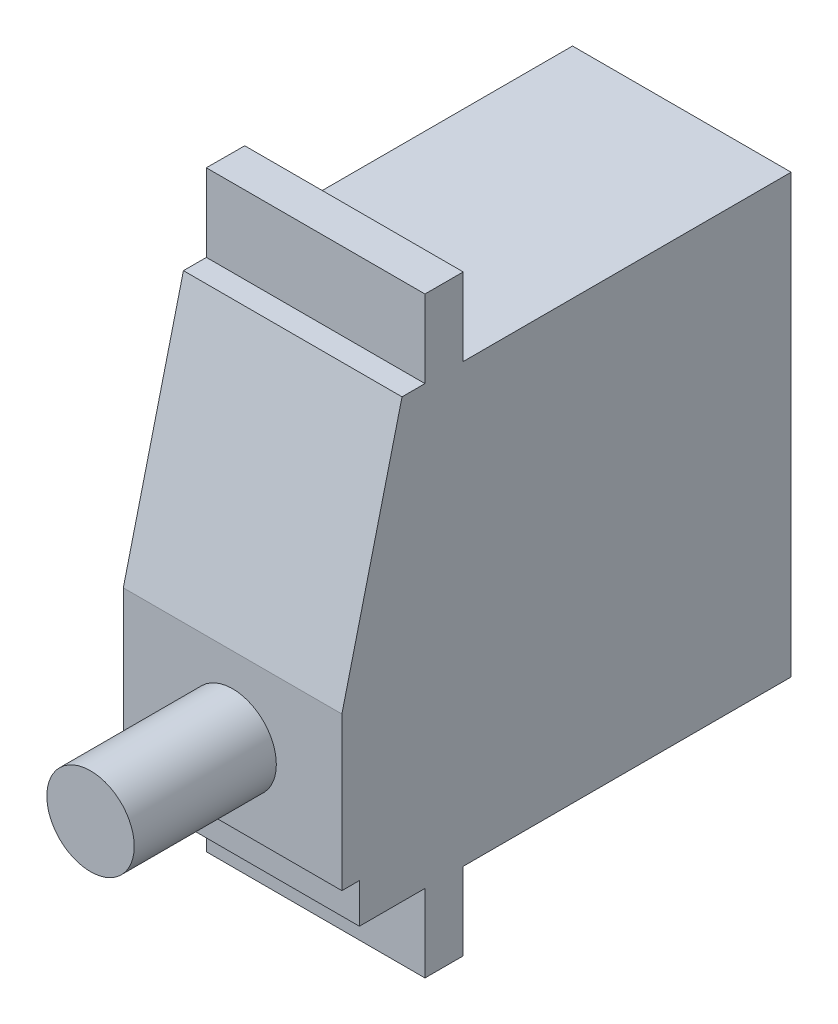
SolidWorks part; units mm, degrees
ref_plane "Front Plane" through (0, 0, 0) normal (0, 0, 1) x (1, 0, 0)
ref_plane "Top Plane" through (0, 0, 0) normal (0, 1, 0) x (1, 0, 0)
ref_plane "Right Plane" through (0, 0, 0) normal (1, 0, 0) x (0, 0, -1)
ref_plane "Plane1" through (10, 0, 0) normal (1, 0, 0) x (0, 0, -1)
sketch "Sketch1" plane through (10, 0, 0) normal (1, 0, 0) x (0, 0, -1)
  line L0 (0, 29.3791) -> (-35.6, 29.3791)
  line L1 (-35.6, 29.3791) -> (-41.1, 7)
  line L2 (-41.1, 7) -> (-41.1, -17.7209)
  line L3 (-41.1, -17.7209) -> (0, -17.7209)
  line L4 (0, -17.7209) -> (0, 29.3791)
extrude "Boss-Extrude1" add sketch "Sketch1" against normal blind 20
sketch "Sketch2" plane through (10, 0, 0) normal (1, 0, 0) x (0, 0, -1)
  line L0 (-30, -10.6209) -> (-30, -17.7209)
  line L1 (-30, -17.7209) -> (0, -17.7209)
  line L2 (0, -17.7209) -> (0, -10.6209)
  line L3 (0, -10.6209) -> (-30, -10.6209)
extrude "Cut-Extrude1" cut sketch "Sketch2" against normal through all
sketch "Sketch3" plane through (10, 0, 0) normal (1, 0, 0) x (0, 0, -1)
  line L0 (-33.5, -10.6209) -> (-41.1, -10.6209)
  line L1 (-41.1, -10.6209) -> (-41.1, -17.7209)
  line L2 (-41.1, -17.7209) -> (-33.5, -17.7209)
  line L3 (-33.5, -17.7209) -> (-33.5, -10.6209)
extrude "Cut-Extrude2" cut sketch "Sketch3" against normal through all
sketch "Sketch4" plane through (10, 0, 0) normal (1, 0, 0) x (0, 0, -1)
  line L0 (-39.5, -7) -> (-41.1, -7)
  line L1 (-41.1, -7) -> (-41.1, -10.6209)
  line L2 (-41.1, -10.6209) -> (-39.5, -10.6209)
  line L3 (-39.5, -10.6209) -> (-39.5, -7)
extrude "Cut-Extrude3" cut sketch "Sketch4" against normal through all
ref_plane "Plane2" through (-9.8732, 0, -0.0388) normal (-1, 0, -0.0039) x (0, -1, 0)
sketch "Sketch6" plane through (10, 0, 0) normal (1, 0, 0) x (0, 0, -1)
  line L0 (-33.5, 29.3791) -> (-30, 29.3791)
  line L1 (-30, 29.3791) -> (-30, 36.4791)
  line L2 (-30, 36.4791) -> (-33.5, 36.4791)
  line L3 (-33.5, 36.4791) -> (-33.5, 29.3791)
extrude "Boss-Extrude2" add sketch "Sketch6" against normal up to surface up to plane "Plane2"
sketch "Sketch7" plane through (0, 0, 41.1) normal (0, 0, 1) x (1, 0, 0)
  circle A0 centre (0, 0) radius 4
  dimension "D1" = 8
extrude "Boss-Extrude3" add sketch "Sketch7" along normal blind 7 contours A0
other "Move Face2" face at (4, 0, 48.1) parameters "D1"=6
